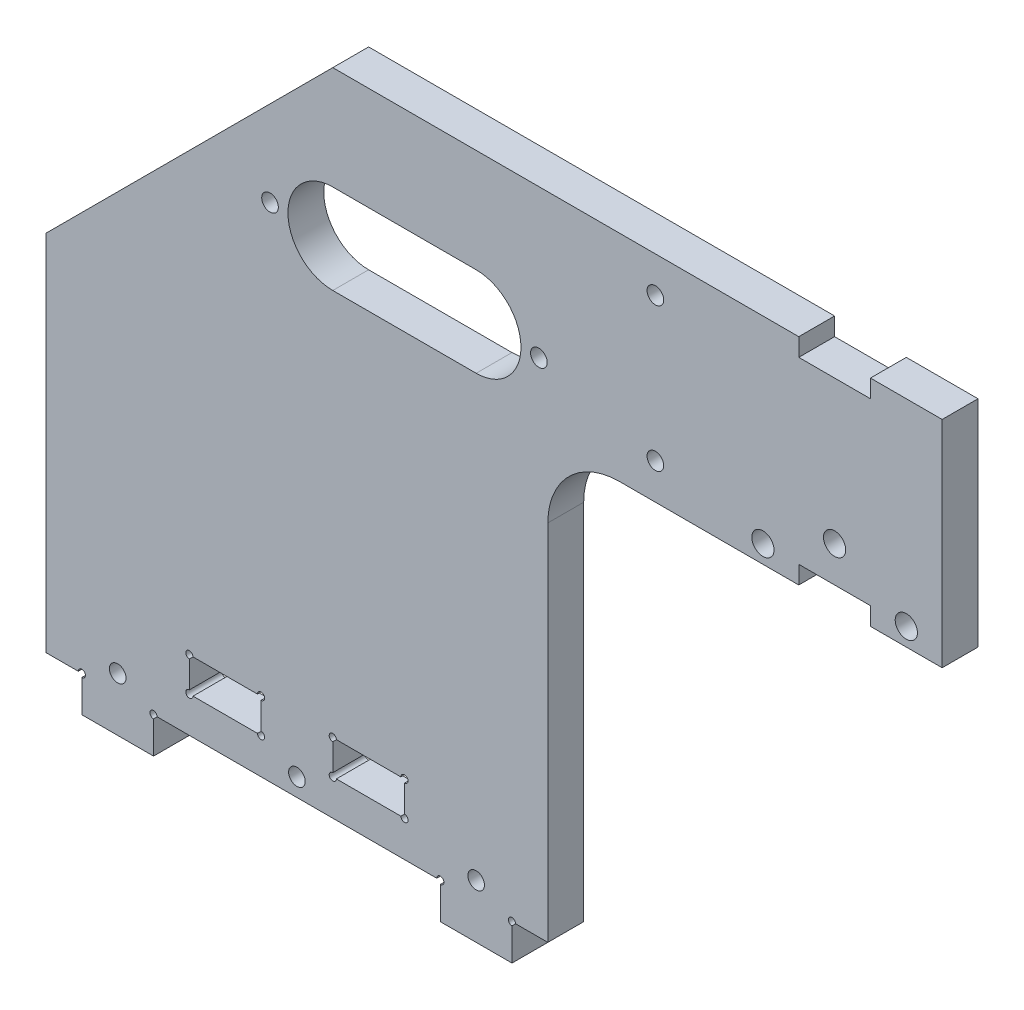
SolidWorks part; units mm, degrees
material "Acrylic (Medium-high impact)"
ref_plane "Front Plane" through (0, 0, 0) normal (0, 0, 1) x (1, 0, 0)
ref_plane "Top Plane" through (0, 0, 0) normal (0, 1, 0) x (1, 0, 0)
ref_plane "Right Plane" through (0, 0, 0) normal (1, 0, 0) x (0, 0, -1)
sketch "Sketch1" plane through (0, 0, 0) normal (0, 0, 1) x (1, 0, 0)
  line L0 (-25.4, 0) -> (25.4, 0)
  line L1 (-25.4, 0) -> (-25.4, -6.35)
  line L2 (-25.4, -6.35) -> (-38.1, -6.35)
  line L3 (-38.1, -6.35) -> (-38.1, 0)
  line L4 (25.4, 0) -> (25.4, -6.35)
  line L5 (25.4, -6.35) -> (38.1, -6.35)
  line L6 (38.1, -6.35) -> (38.1, 0)
  line L7 (-38.1, 0) -> (-44.45, 0)
  line L8 (-44.45, 115.152) -> (88.9, 115.152)
  line L9 (114.3, 115.152) -> (114.3, 77.052)
  line L10 (114.3, 77.052) -> (101.6, 77.052)
  line L11 (38.1, 0) -> (44.45, 0)
  line L12 (82.55, -6.35) -> (107.95, -6.35) construction
  line L13 (44.45, -6.35) -> (69.85, -6.35) construction
  line L14 (44.45, -6.35) -> (44.45, -31.75) construction
  line L15 (44.45, -31.75) -> (69.85, -31.75) construction
  line L16 (69.85, -6.35) -> (69.85, -31.75) construction
  line L17 (44.45, -6.35) -> (69.85, -31.75) construction
  line L18 (44.45, -31.75) -> (69.85, -6.35) construction
  line L19 (82.55, -6.35) -> (82.55, -31.75) construction
  line L20 (82.55, -31.75) -> (107.95, -31.75) construction
  line L21 (107.95, -6.35) -> (107.95, -31.75) construction
  line L22 (82.55, -6.35) -> (107.95, -31.75) construction
  line L23 (82.55, -31.75) -> (107.95, -6.35) construction
  line L24 (-44.45, 0) -> (-44.45, 115.152)
  line L25 (74.25, 58.002) -> (116.25, 58.002) construction
  line L26 (74.25, 58.002) -> (74.25, 16.002) construction
  line L27 (74.25, 16.002) -> (116.25, 16.002) construction
  line L28 (116.25, 58.002) -> (116.25, 16.002) construction
  line L29 (74.25, 58.002) -> (116.25, 16.002) construction
  line L30 (74.25, 16.002) -> (116.25, 58.002) construction
  line L31 (44.45, 0) -> (44.45, 77.052)
  line L32 (6.35, 12.3698) -> (19.05, 12.3698)
  line L33 (-19.05, 12.3698) -> (-6.35, 12.3698)
  line L34 (-19.05, 12.3698) -> (-19.05, 6.35)
  line L35 (-19.05, 6.35) -> (-6.35, 6.35)
  line L36 (-6.35, 12.3698) -> (-6.35, 6.35)
  line L37 (-19.05, 12.3698) -> (-6.35, 6.35) construction
  line L38 (-19.05, 6.35) -> (-6.35, 12.3698) construction
  line L39 (6.35, 12.3698) -> (6.35, 6.35)
  line L40 (6.35, 6.35) -> (19.05, 6.35)
  line L41 (19.05, 12.3698) -> (19.05, 6.35)
  line L42 (6.35, 12.3698) -> (19.05, 6.35) construction
  line L43 (6.35, 6.35) -> (19.05, 12.3698) construction
  line L44 (95.25, 37.002) -> (95.25, 80.227) construction
  line L45 (104.775, 102.452) -> (107.95, 102.452) construction
  line L46 (104.775, 102.452) -> (104.775, 89.752) construction
  line L47 (104.775, 89.752) -> (107.95, 89.752) construction
  line L48 (107.95, 102.452) -> (107.95, 89.752) construction
  line L49 (104.775, 102.452) -> (107.95, 89.752) construction
  line L50 (104.775, 89.752) -> (107.95, 102.452) construction
  line L51 (85.725, 89.752) -> (82.55, 102.452) construction
  line L52 (85.725, 102.452) -> (82.55, 89.752) construction
  line L53 (82.55, 102.452) -> (82.55, 89.752) construction
  line L54 (85.725, 89.752) -> (82.55, 89.752) construction
  line L55 (85.725, 102.452) -> (85.725, 89.752) construction
  line L56 (85.725, 102.452) -> (82.55, 102.452) construction
  line L57 (101.6, 115.152) -> (114.3, 115.152)
  line L58 (114.3, 96.102) -> (92.4514, 96.102) construction
  line L59 (88.9, 115.152) -> (88.9, 111.977)
  line L60 (88.9, 111.977) -> (101.6, 111.977)
  line L61 (101.6, 115.152) -> (101.6, 111.977)
  line L62 (101.6, 77.052) -> (101.6, 80.227)
  line L63 (88.9, 80.227) -> (101.6, 80.227)
  line L64 (88.9, 77.052) -> (88.9, 80.227)
  line L65 (88.9, 77.052) -> (44.45, 77.052)
  line L66 (95.25, 111.977) -> (95.25, 80.227) construction
  line L67 (-12.7, 9.3599) -> (12.7, 9.3599) construction
  point P1 (12.7, 9.3599)
  point P9 (57.15, -19.05)
  point P11 (-12.7, 9.3599)
  point P16 (0, 9.3599)
  point P20 (95.25, -19.05)
  point P25 (95.25, 37.002)
  point P43 (106.3625, 96.102)
  point P75 (84.1375, 96.102)
  point P76 (114.3, 96.102)
  point P81 (95.25, 111.977)
  dimension "D19" = 6.35
  dimension "D20" = 6.0198
  dimension "D21" = 19.05
  dimension "D3" = 12.7
  dimension "D4" = 12.7
  dimension "D5" = 50.8
  dimension "D6" = 6.35
  dimension "D7" = 25.4
  dimension "D8" = 25.4
  dimension "D9" = 31.75
  dimension "D10" = 25.4
  dimension "D11" = 25.4
  dimension "D12" = 38.1
  dimension "D13" = 38.1
  dimension "D14" = 42
  dimension "D15" = 42
  dimension "D16" = 22.352
  dimension "D17" = 19.05
  dimension "D18" = 6.35
  dimension "D22" = 3.175
  dimension "D23" = 12.7
  dimension "D24" = 6.35
  dimension "D25" = 12.7
  dimension "D26" = 3.175
  dimension "D27" = 12.7
  dimension "D28" = 12.7
  dimension "D29" = 25.4
extrude "Boss-Extrude1" add sketch "Sketch1" along normal blind 6.35
sketch "Sketch10" plane through (0, 0, 0) normal (0, 0, 1) x (1, 0, 0)
  line L0 (-6.35, 6.35) -> (-6.35, 12.3698) construction
  line L1 (-6.35, 12.3698) -> (-19.05, 12.3698) construction
  line L2 (25.4, 0) -> (25.4, -6.35) construction
  line L3 (-25.4, 0) -> (25.4, 0) construction
  line L4 (-38.1, 0) -> (-38.1, -6.35) construction
  point P0 (-19.05, 12.3698)
  point P1 (-6.35, 12.3698)
  point P3 (-6.35, 6.35)
  point P8 (-19.05, 6.35)
  point P9 (6.35, 12.3698)
  point P11 (19.05, 12.3698)
  point P13 (19.05, 6.35)
  point P15 (6.35, 6.35)
  point P17 (38.1, 0)
  point P19 (25.4, 0)
  point P21 (-25.4, 0)
  point P26 (-38.1, 0)
sketch "Sketch13" plane through (0, 0, 0) normal (0, 0, 1) x (1, 0, 0)
  circle A0 centre (-19.05, 12.3698) radius 0.635
  dimension "D1" = 1.27
extrude "Cut-Extrude2" cut sketch "Sketch13" along normal up to next
pattern_sketch "Sketch-Pattern1" of "Cut-Extrude2" driven by "Sketch10"
chamfer "Chamfer1" distance 50.8 angle 45 1 edges at (-44.45, 115.152, 3.175)
fillet "Fillet2" radius 12.7 1 edges at (44.45, 77.052, 3.175)
sketch "Sketch5" plane through (0, 0, 6.35) normal (0, 0, 1) x (1, 0, 0)
  line L0 (-34.925, 21.0399) -> (-34.925, 0)
  line L1 (-28.575, 21.0399) -> (-28.575, 1.5959)
  line L2 (-34.925, 16.0499) -> (-28.575, 16.0499) construction
  line L3 (-31.75, 16.0499) -> (-31.75, -6.35) construction
  line L5 (-24.765, 0) -> (24.765, 0) construction
  line L6 (-20.9887, 3.175) -> (-22.8217, 6.35)
  line L7 (-22.8217, 6.35) -> (-26.4879, 6.35)
  line L8 (-26.4879, 6.35) -> (-28.321, 3.175)
  line L9 (-28.321, 3.175) -> (-26.4879, 0)
  line L10 (-26.4879, 0) -> (-22.8217, 0)
  line L11 (-22.8217, 0) -> (-20.9887, 3.175)
  line L12 (0, 0) -> (0, 13.7358) construction
  line L13 (-38.1, -6.35) -> (-25.4, -6.35) construction
  circle A0 centre (-24.6548, 3.175) radius 3.175 construction
  point P21 (-38.8452, 3.175)
  point P23 (24.6548, 3.175)
  point P24 (38.8452, 3.175)
  dimension "D1" = 6.35
  dimension "D2" = 6.35
  dimension "D3" = 0.254
hole_wizard "#4 Clearance Hole1" positions "Sketch7" profile "Sketch6" hole size "#4" standard "ANSI Inch"
sketch "Sketch7" plane through (0, 0, 6.35) normal (0, 0, 1) x (1, 0, 0)
  line L0 (25.4, -6.35) -> (38.1, -6.35) construction
  line L1 (-38.1, -6.35) -> (-25.4, -6.35) construction
  line L2 (-38.8452, 3.175) -> (31.75, 3.175) construction
  line L4 (-31.75, 16.0499) -> (-31.75, -6.35) construction
  point P4 (-31.75, 3.175)
  point P7 (31.75, 3.175)
  point P10 (0, 3.175)
  point P20 (31.75, -6.35)
  point P23 (-31.75, -6.35)
sketch "Sketch6" plane through (-31.75, 3.175, 6.35) normal (1, 0, 0) x (0, -1, 0)
  line L0 (0, 0) -> (0, 7.2352)
  line L1 (0, 7.2352) -> (1.4732, 6.35)
  line L2 (1.4732, 6.35) -> (1.4732, 0)
  line L5 (1.4732, 0) -> (0, 0)
  line L10 (0, 7.2352) -> (-1.4732, 6.35) construction
  line L11 (0, -6.35) -> (0, 107.95) construction
  dimension "Hole Dia." = 2.9464
  dimension "Hole Depth" = 6.35
  dimension "Drill Angle" = 118
sketch "Sketch8" plane through (0, 0, 6.35) normal (0, 0, 1) x (1, 0, 0)
  line L0 (63.5, 115.152) -> (63.5, 77.052) construction
  line L1 (88.9, 115.152) -> (6.35, 115.152) construction
  line L2 (57.15, 77.052) -> (88.9, 77.052) construction
  line L3 (114.3, 77.052) -> (114.3, 115.152) construction
  line L4 (63.5, 108.802) -> (63.5, 83.402) construction
  line L5 (63.5, 112.4682) -> (60.325, 110.6351)
  line L6 (60.325, 110.6351) -> (60.325, 106.9689)
  line L7 (60.325, 106.9689) -> (63.5, 105.1358)
  line L8 (63.5, 105.1358) -> (66.675, 106.9689)
  line L9 (66.675, 106.9689) -> (66.675, 110.6351)
  line L10 (66.675, 110.6351) -> (63.5, 112.4682)
  line L11 (63.5, 79.7358) -> (66.675, 81.5689)
  line L12 (66.675, 81.5689) -> (66.675, 85.2351)
  line L13 (66.675, 85.2351) -> (63.5, 87.0682)
  line L14 (63.5, 87.0682) -> (60.325, 85.2351)
  line L15 (60.325, 85.2351) -> (60.325, 81.5689)
  line L16 (60.325, 81.5689) -> (63.5, 79.7358)
  circle A0 centre (63.5, 108.802) radius 3.175 construction
  circle A1 centre (63.5, 83.402) radius 3.175 construction
  point P8 (63.5, 108.802)
  point P9 (63.5, 83.402)
  dimension "D1" = 50.8
  dimension "D2" = 6.35
  dimension "D3" = 6.35
  dimension "D4" = 25.4
sketch "Sketch14" plane through (0, 0, 6.35) normal (0, 0, 1) x (1, 0, 0)
  line L0 (76.2, 80.227) -> (114.3, 80.227) construction
  line L1 (88.9, 80.227) -> (101.6, 80.227) construction
  line L2 (114.3, 77.052) -> (101.6, 77.052) construction
  line L3 (95.25, 37.002) -> (95.25, 80.227) construction
  line L4 (95.25, 80.227) -> (95.25, 77.7878) construction
  circle A0 centre (95.25, 86.577) radius 1.9685
  circle A1 centre (82.55, 80.227) radius 1.9685
  circle A2 centre (107.95, 80.227) radius 1.9685
  circle A3 centre (82.55, 80.227) radius 2.794 construction
  circle A4 centre (95.25, 86.577) radius 2.794 construction
  point P2 (95.25, 80.227)
  dimension "D2" = 3.937
  dimension "D3" = 9.525
  dimension "D4" = 25.4
  dimension "D5" = 5.588
  dimension "D1" = 38.1
extrude "Cut-Extrude3" cut sketch "Sketch14" against normal up to next
hole_wizard "#4 Clearance Hole2" positions "Sketch17" profile "Sketch16" hole size "#4" standard "ANSI Inch"
sketch "Sketch17" plane through (0, 0, 6.35) normal (0, 0, 1) x (1, 0, 0)
  point P0 (63.5, 83.402)
  point P3 (63.5, 108.802)
sketch "Sketch16" plane through (63.5, 83.402, 6.35) normal (1, 0, 0) x (0, -1, 0)
  line L0 (0, 0) -> (0, 7.2352)
  line L1 (0, 7.2352) -> (1.4732, 6.35)
  line L2 (1.4732, 6.35) -> (1.4732, 0)
  line L5 (1.4732, 0) -> (0, 0)
  line L10 (0, 7.2352) -> (-1.4732, 6.35) construction
  line L11 (0, -6.35) -> (0, 107.95) construction
  dimension "Hole Dia." = 2.9464
  dimension "Hole Depth" = 6.35
  dimension "Drill Angle" = 118
sketch "Sketch18" plane through (0, 0, 6.35) normal (0, 0, 1) x (1, 0, 0)
  line L0 (6.35, 88.9) -> (31.75, 88.9) construction
  line L1 (6.35, 96.8375) -> (31.75, 96.8375)
  line L2 (6.35, 80.9625) -> (31.75, 80.9625)
  line L4 (-24.765, 0) -> (24.765, 0) construction
  line L5 (-24.765, 0) -> (24.765, 0) construction
  arc A0 (6.35, 96.8375) -> (6.35, 80.9625) centre (6.35, 88.9) ccw
  arc A1 (31.75, 80.9625) -> (31.75, 96.8375) centre (31.75, 88.9) ccw
  point P2 (19.05, 88.9)
  point P9 (0, 0)
  dimension "D1" = 25.4
  dimension "D2" = 15.875
  dimension "D3" = 88.9
  dimension "D4" = 19.05
extrude "Cut-Extrude4" cut sketch "Sketch18" against normal up to next
hole_wizard "#4 Clearance Hole3" positions "Sketch20" profile "Sketch19" hole size "#4" standard "ANSI Inch"
sketch "Sketch20" plane through (0, 0, 6.35) normal (0, 0, 1) x (1, 0, 0)
  line L0 (6.35, 88.9) -> (31.75, 88.9) construction
  arc A0 (6.35, 96.8375) -> (6.35, 80.9625) centre (6.35, 88.9) ccw construction
  arc A1 (31.75, 80.9625) -> (31.75, 96.8375) centre (31.75, 88.9) ccw construction
  point P0 (-4.7625, 88.9)
  point P2 (42.8625, 88.9)
  dimension "D1" = 3.175
  dimension "D2" = 3.175
sketch "Sketch19" plane through (-4.7625, 88.9, 6.35) normal (1, 0, 0) x (0, -1, 0)
  line L0 (0, 0) -> (0, 7.2352)
  line L1 (0, 7.2352) -> (1.4732, 6.35)
  line L2 (1.4732, 6.35) -> (1.4732, 0)
  line L5 (1.4732, 0) -> (0, 0)
  line L10 (0, 7.2352) -> (-1.4732, 6.35) construction
  line L11 (0, -6.35) -> (0, 107.95) construction
  dimension "Hole Dia." = 2.9464
  dimension "Hole Depth" = 6.35
  dimension "Drill Angle" = 118
